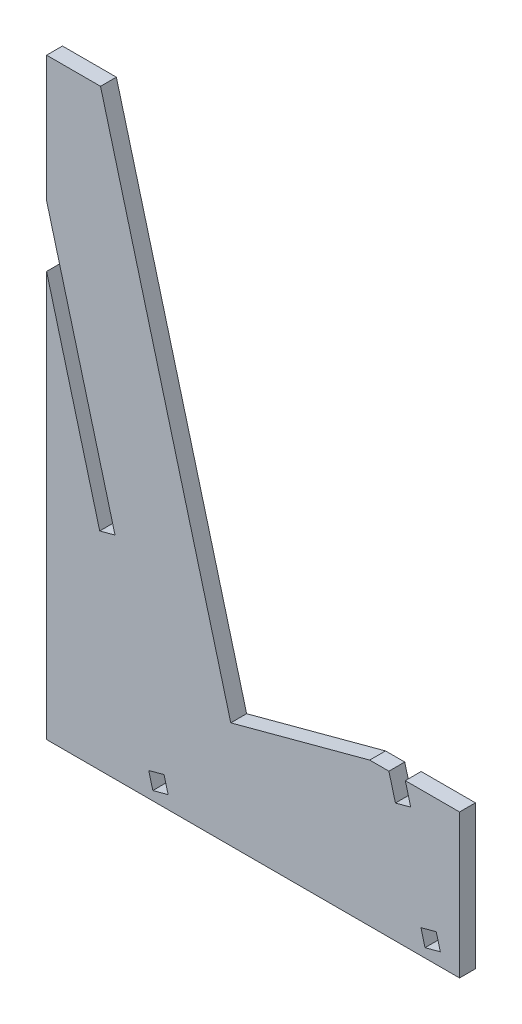
SolidWorks part; units mm, degrees
ref_plane "Front Plane" through (0, 0, 0) normal (0, 0, 1) x (1, 0, 0)
ref_plane "Top Plane" through (0, 0, 0) normal (0, 1, 0) x (1, 0, 0)
ref_plane "Right Plane" through (0, 0, 0) normal (1, 0, 0) x (0, 0, -1)
sketch "Sketch1" plane through (0, 0, 0) normal (0, 0, 1) x (1, 0, 0)
  line L0 (-38.029, 83.6028) -> (-38.029, -21.094)
  line L1 (-38.029, -21.094) -> (34.9145, -21.094)
  line L2 (34.9145, -21.094) -> (34.9145, 4.306)
  line L3 (34.9145, 4.306) -> (19.0395, 4.306)
  line L4 (19.0395, 4.306) -> (-5.495, -2.268)
  line L5 (-5.495, -2.268) -> (-28.504, 83.6028)
  line L6 (-28.504, 83.6028) -> (-38.029, 83.6028)
  dimension "D1" = 25.4
  dimension "D2" = 25.4
  dimension "D3" = 88.9
  dimension "D4" = 15.875
  dimension "D5" = 9.525
  dimension "D6" = 15
extrude "Boss-Extrude1" add sketch "Sketch1" along normal blind 2.8
sketch "Sketch2" plane through (0, 0, 2.8) normal (0, 0, 1) x (1, 0, 0)
  line L0 (-19.2646, -19.5065) -> (-16.5601, -18.7818)
  line L1 (-19.2646, -19.5065) -> (-19.9893, -16.8019)
  line L2 (-16.5601, -18.7818) -> (-17.2847, -16.0772)
  line L3 (-19.9893, -16.8019) -> (-17.2847, -16.0772)
  line L4 (-19.2646, -19.5065) -> (-17.2847, -16.0772) construction
  line L5 (-16.5601, -18.7818) -> (-19.9893, -16.8019) construction
  line L6 (-5.495, -2.268) -> (-28.504, 83.6028) construction
  line L7 (-38.029, -21.094) -> (34.9145, -21.094) construction
  line L8 (-28.6468, 15.5083) -> (-25.9422, 16.233)
  line L9 (-28.6468, 15.5083) -> (-38.029, 50.5231)
  line L10 (-25.9422, 16.233) -> (-35.3244, 51.2478)
  line L11 (-38.029, 50.5231) -> (-35.3244, 51.2478) construction
  line L12 (-28.6468, 15.5083) -> (-35.3244, 51.2478) construction
  line L13 (-25.9422, 16.233) -> (-38.029, 50.5231) construction
  line L14 (-38.029, 83.6028) -> (-38.029, -21.094) construction
  line L15 (-19.2646, -19.5065) -> (-38.029, 50.5231) construction
  line L16 (-35.3244, 51.2478) -> (-38.029, 61.3415)
  line L17 (-38.029, 61.3415) -> (-38.029, 50.5231)
  line L18 (-30.7938, 28.93) -> (-23.029, -0.0485) construction
  point P0 (-28.6468, 15.5083)
  point P1 (-18.2747, -17.7919)
  point P10 (-31.9856, 33.378)
  dimension "D1" = 2.8
  dimension "D2" = 2.8
  dimension "D3" = 1.5875
  dimension "D4" = 2.8
  dimension "D5" = 72.5
extrude "Cut-Extrude1" cut sketch "Sketch2" against normal through all
sketch "Sketch3" plane through (0, 0, 2.8) normal (0, 0, 1) x (1, 0, 0)
  line L0 (28.815, -19.5065) -> (31.5196, -18.7818)
  line L1 (28.815, -19.5065) -> (28.0903, -16.8019)
  line L2 (31.5196, -18.7818) -> (30.7949, -16.0772)
  line L3 (28.0903, -16.8019) -> (30.7949, -16.0772)
  line L4 (28.815, -19.5065) -> (30.7949, -16.0772) construction
  line L5 (31.5196, -18.7818) -> (28.0903, -16.8019) construction
  line L6 (23.5862, 0.0074) -> (26.2908, 0.7321)
  line L7 (23.5862, 0.0074) -> (22.6286, 3.5813)
  line L8 (26.2908, 0.7321) -> (25.3332, 4.306)
  line L9 (22.6286, 3.5813) -> (25.3332, 4.306) construction
  line L10 (23.5862, 0.0074) -> (25.3332, 4.306) construction
  line L11 (26.2908, 0.7321) -> (22.6286, 3.5813) construction
  line L12 (-5.495, -2.268) -> (-28.504, 83.6028) construction
  line L15 (34.9145, 4.306) -> (19.0395, 4.306) construction
  line L16 (22.6286, 3.5813) -> (22.4344, 4.306)
  line L17 (22.4344, 4.306) -> (25.3332, 4.306)
  line L18 (22.6286, 3.5813) -> (28.815, -19.5065) construction
  line L19 (19.0395, 4.306) -> (22.4344, 4.306) construction
  line L20 (31.5196, -18.7818) -> (34.9145, -18.7818) construction
  line L21 (34.9145, -21.094) -> (34.9145, 4.306) construction
  point P1 (29.8049, -17.7919)
  point P2 (24.4597, 2.1567)
  dimension "D1" = 2.8
  dimension "D2" = 2.8
  dimension "D3" = 3.7
extrude "Cut-Extrude2" cut sketch "Sketch3" against normal through all
equation "\"thick\"= 2.80mm"
equation "\"D1@Boss-Extrude1\"=\"thick\""
equation "\"D1@Sketch2\"=\"thick\""
equation "\"D2@Sketch2\"=\"thick\""
equation "\"D4@Sketch2\"=\"thick\""
equation "\"D1@Sketch3\"=\"thick\""
equation "\"D2@Sketch3\"=\"thick\""
